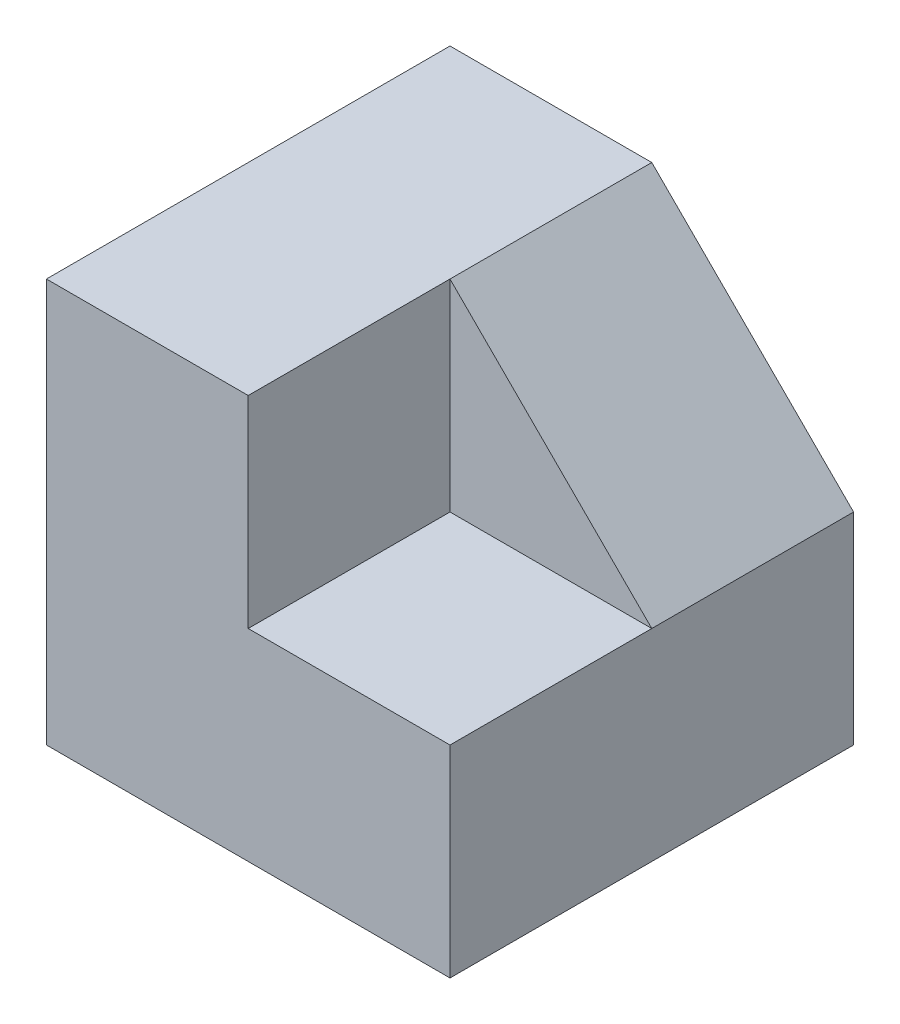
SolidWorks part; units mm, degrees
ref_plane "Alzado" through (0, 0, 0) normal (0, 0, 1) x (1, 0, 0)
ref_plane "Planta" through (0, 0, 0) normal (0, 1, 0) x (1, 0, 0)
ref_plane "Vista lateral" through (0, 0, 0) normal (1, 0, 0) x (0, 0, -1)
sketch "Croquis1" plane through (0, 0, 0) normal (0, 1, 0) x (1, 0, 0)
  line L1 (0, 0) -> (60, 0)
  line L2 (0, 0) -> (0, -60)
  line L3 (0, -60) -> (60, -60)
  line L4 (60, 0) -> (60, -60)
  dimension "D1" = 60
  dimension "D2" = 60
extrude "Saliente-Extruir1" add sketch "Croquis1" along normal blind 60
sketch "Croquis2" plane through (0, 60, 0) normal (0, 1, 0) x (1, 0, 0)
  line L1 (60, -60) -> (30, -60)
  line L2 (60, -60) -> (60, -30)
  line L3 (60, -30) -> (30, -30)
  line L4 (30, -60) -> (30, -30)
  dimension "D1" = 30
  dimension "D2" = 30
extrude "Cortar-Extruir1" cut sketch "Croquis2" against normal blind 30
sketch "Croquis3" plane through (0, 0, 30) normal (0, 0, 1) x (1, 0, 0)
  line L0 (30, 60) -> (60, 30)
  line L1 (60, 30) -> (60, 60)
  line L2 (60, 60) -> (30, 60)
extrude "Cortar-Extruir2" cut sketch "Croquis3" against normal blind 30
